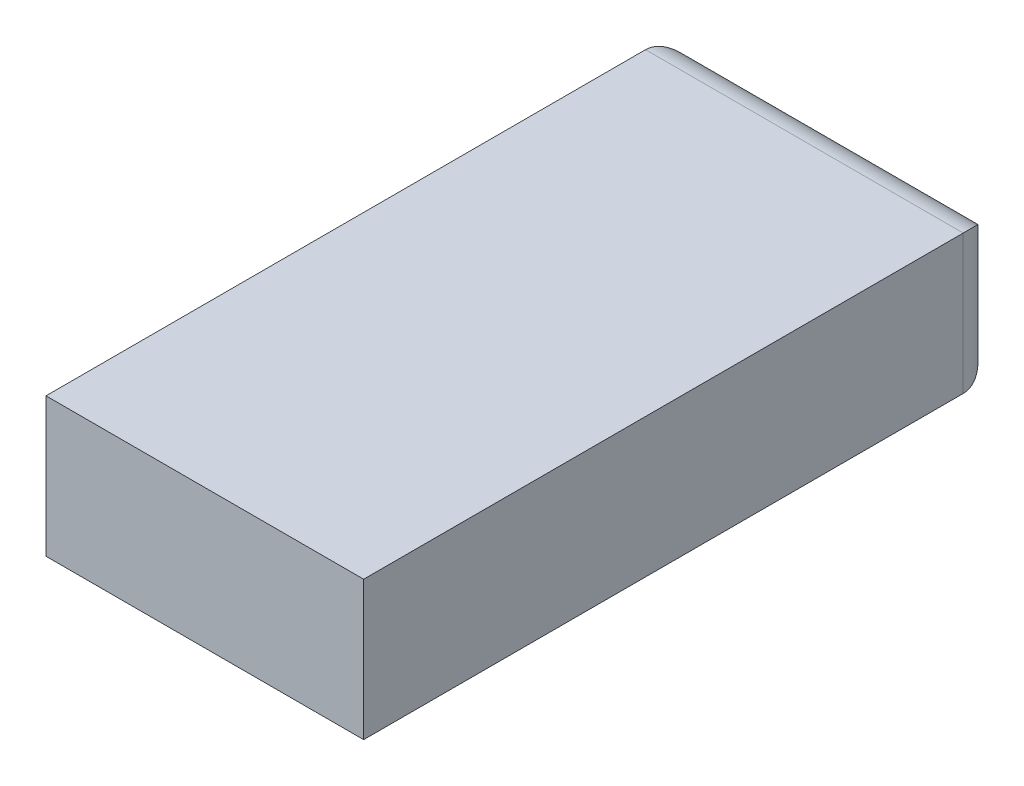
SolidWorks part; units mm, degrees
material "PE High Density Film"
ref_plane "Front Plane" through (0, 0, 0) normal (0, 0, 1) x (1, 0, 0)
ref_plane "Top Plane" through (0, 0, 0) normal (0, 1, 0) x (1, 0, 0)
ref_plane "Right Plane" through (0, 0, 0) normal (1, 0, 0) x (0, 0, -1)
sketch "Sketch1" plane through (0, 0, 0) normal (0, 1, 0) x (1, 0, 0)
  line L1 (-50.8, -101.6) -> (50.8, -101.6)
  line L2 (-50.8, -101.6) -> (-50.8, 101.6)
  line L3 (-50.8, 101.6) -> (50.8, 101.6)
  line L4 (50.8, -101.6) -> (50.8, 101.6)
  line L5 (-50.8, -101.6) -> (50.8, 101.6) construction
  line L6 (-50.8, 101.6) -> (50.8, -101.6) construction
  point P0 (0, 0)
  dimension "D1" = 203.2
  dimension "D2" = 101.6
extrude "Boss-Extrude1" add sketch "Sketch1" along normal blind 44.45
fillet "Fillet1" radius 11.43 4 edges at (50.8, 22.225, -101.6) (0, 44.45, -101.6) (-50.8, 22.225, -101.6) (0, 0, -101.6)
